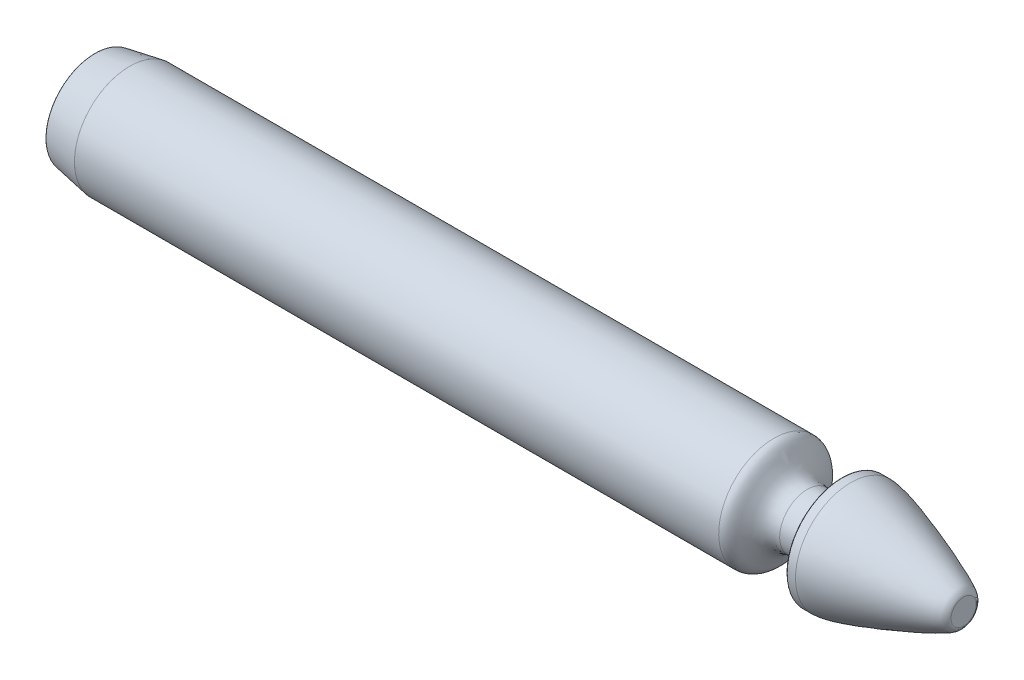
SolidWorks part; units mm, degrees
material "Stainless Steel (ferritic)"
ref_plane "Front" through (0, 0, 0) normal (0, 0, 1) x (1, 0, 0)
ref_plane "Top" through (0, 0, 0) normal (0, 1, 0) x (1, 0, 0)
ref_plane "Right" through (0, 0, 0) normal (1, 0, 0) x (0, 0, -1)
sketch "body_sketch" plane through (0, 0, 0) normal (0, 0, 1) x (1, 0, 0)
  line L1 (-16.7357, 3.175) -> (-10.9218, 3.175)
  line L2 (-48, 3.175) -> (-20.8111, 3.175)
  line L3 (-19.1074, 3.175) -> (-22.5343, 3.175) construction
  line L4 (-6.5, 3.175) -> (-7, 3.175)
  line L5 (-15.6683, 3.175) -> (-17.809, 3.175) construction
  line L6 (-50, 0) -> (-50, 2.8223)
  line L7 (-50, 2.8223) -> (-48, 3.175)
  line L9 (-7, 3.175) -> (-7, 1.5875)
  line L10 (-7, 1.5875) -> (-9, 1.5875)
  line L13 (14.3233, 1.5875) -> (12.3233, 1.5875) construction
  line L14 (-10.9218, 3.175) -> (-7, 3.175) construction
  line L15 (0, 0) -> (-50, 0)
  line L17 (0, 0.7246) -> (0, 0)
  spline S0 degree 3 poles (-6.5, 3.175) (-5.4841, 3.175) (-0.421, 1.3023) (-0.0097, 0.8171) (0, 0.774) (0, 0.7246) knots 0 0 0 0 0.586138 0.686138 1 1 1 1
  spline S1 degree 3 poles (-10.9218, 3.175) (-10.1654, 3.175) (-10.25, 1.5875) (-9, 1.5875) knots 0 0 0 0 1 1 1 1
  spline S2 degree 3 poles (-20.8111, 3.175) (-19.3832, 3.175) (-18.0736, 3.175) (-16.7357, 3.175) knots 0 0 0 0 1 1 1 1
  point P5 (-48, -3.175)
  dimension "D1" = 6.35
  dimension "D2" = 0.5
  dimension "D3" = 2
  dimension "D4" = 1.5875
  dimension "D5" = 50
  dimension "D6" = 7
  dimension "D7" = 3.175
  dimension "D8" = 10
  dimension "D9" = 2
revolve "body" add sketch "body_sketch" angle 360 about L15
sketch "minimum_diameter" plane through (0, 0, 0) normal (1, 0, 0) x (0, 0, -1)
  circle A0 centre (0, 0) radius 1.5875 construction
  circle A2 centre (0, 0) radius 1.5875 construction
fillet "break_edges" radius 0.02 3 edges at (-50, 2.8223, 0) (-48, 3.175, 0) (-7, 3.175, 0)
